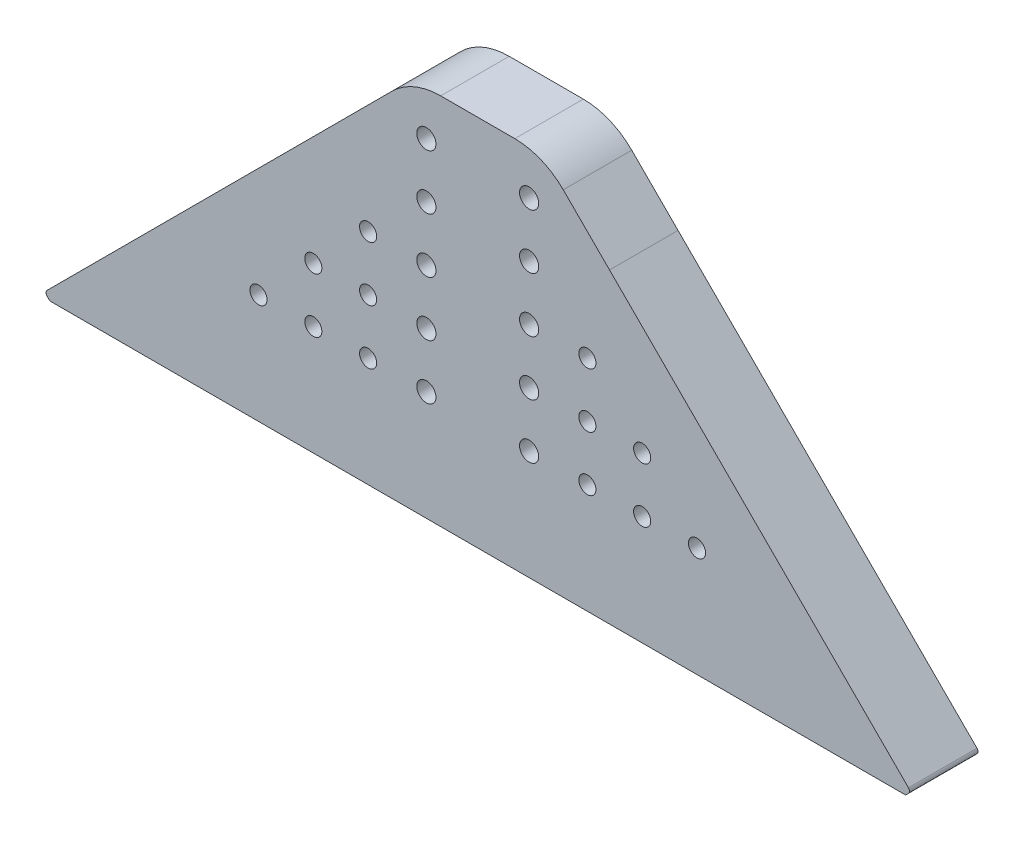
SolidWorks part; units mm, degrees
ref_plane "前视基准面" through (0, 0, 0) normal (0, 0, 1) x (1, 0, 0)
ref_plane "上视基准面" through (0, 0, 0) normal (0, 1, 0) x (1, 0, 0)
ref_plane "右视基准面" through (0, 0, 0) normal (1, 0, 0) x (0, 0, -1)
sketch "草图3" plane through (0, 0, 0) normal (0, 0, 1) x (1, 0, 0)
  line L0 (1203.2316, 480.4049) -> (1082.7316, 480.4049)
  line L1 (1082.7316, 480.4049) -> (1082.3101, 480.8263)
  line L2 (1082.3101, 481.5334) -> (1132.7027, 531.9259)
  line L3 (1203.2316, 480.4049) -> (1207.6316, 480.4049)
  line L4 (1150.5895, 534.8549) -> (1139.7737, 534.8549)
  line L5 (1164.4183, 525.1681) -> (1157.6605, 531.9259)
  line L6 (1208.053, 481.5334) -> (1164.4183, 525.1681)
  line L7 (1207.6316, 480.4049) -> (1208.053, 480.8263)
  circle A0 centre (1113.1816, 496.4049) radius 1.25
  circle A1 centre (1121.1816, 496.4049) radius 1.25
  circle A2 centre (1129.1816, 512.4049) radius 1.25
  circle A3 centre (1129.1816, 504.4049) radius 1.25
  circle A4 centre (1129.1816, 496.4049) radius 1.25
  circle A5 centre (1121.1816, 504.4049) radius 1.25
  arc A6 (1082.3101, 481.5334) -> (1082.3101, 480.8263) centre (1082.6637, 481.1799) ccw
  circle A7 centre (1169.1816, 504.4049) radius 1.25
  circle A8 centre (1161.1816, 496.4049) radius 1.25
  circle A9 centre (1161.1816, 504.4049) radius 1.25
  circle A10 centre (1161.1816, 512.4049) radius 1.25
  circle A11 centre (1169.1816, 496.4049) radius 1.25
  circle A12 centre (1177.1816, 496.4049) radius 1.25
  arc A13 (1139.7737, 534.8549) -> (1132.7027, 531.9259) centre (1139.7737, 524.8549) ccw
  arc A14 (1157.6605, 531.9259) -> (1150.5895, 534.8549) centre (1150.5895, 524.8549) ccw
  arc A15 (1208.053, 480.8263) -> (1208.053, 481.5334) centre (1207.6995, 481.1799) ccw
  circle A16 centre (1137.6816, 496.4049) radius 1.4
  circle A17 centre (1152.6816, 496.4049) radius 1.4
  circle A18 centre (1137.6816, 504.4049) radius 1.4
  circle A19 centre (1152.6816, 504.4049) radius 1.4
  circle A20 centre (1137.6816, 512.4049) radius 1.4
  circle A21 centre (1152.6816, 512.4049) radius 1.4
  circle A22 centre (1137.6816, 520.4049) radius 1.4
  circle A23 centre (1152.6816, 520.4049) radius 1.4
  circle A24 centre (1137.6816, 528.4049) radius 1.4
  circle A25 centre (1152.6816, 528.4049) radius 1.4
extrude "凸台-拉伸2" add sketch "草图3" along normal blind 10
